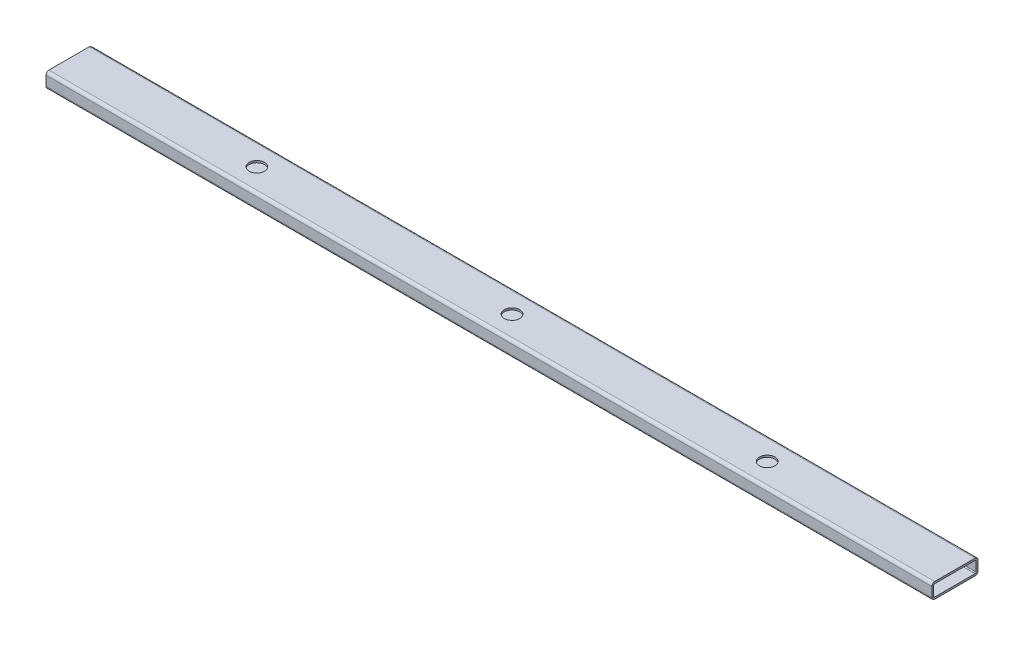
SolidWorks part; units mm, degrees
ref_plane "Front Plane" through (0, 0, 0) normal (0, 0, 1) x (1, 0, 0)
ref_plane "Top Plane" through (0, 0, 0) normal (0, 1, 0) x (1, 0, 0)
ref_plane "Right Plane" through (0, 0, 0) normal (1, 0, 0) x (0, 0, -1)
sketch "Sketch1" plane through (0, 0, 0) normal (1, 0, 0) x (0, 0, -1)
  line L0 (33.3248, 22.225) -> (-33.3248, 22.225)
  line L1 (33.3248, 25.4) -> (-33.3248, 25.4)
  line L2 (38.1, 20.6248) -> (38.1, 4.7752)
  line L3 (33.3248, 0) -> (-33.3248, 0)
  line L4 (-38.1, 20.6248) -> (-38.1, 4.7752)
  line L5 (-34.925, 20.6248) -> (-34.925, 4.7752)
  line L6 (33.3248, 3.175) -> (-33.3248, 3.175)
  line L7 (34.925, 20.6248) -> (34.925, 4.7752)
  arc A0 (38.1, 20.6248) -> (33.3248, 25.4) centre (33.3248, 20.6248) ccw
  arc A1 (38.1, 4.7752) -> (33.3248, 0) centre (33.3248, 4.7752) cw
  arc A2 (-33.3248, 0) -> (-38.1, 4.7752) centre (-33.3248, 4.7752) cw
  arc A3 (-38.1, 20.6248) -> (-33.3248, 25.4) centre (-33.3248, 20.6248) cw
  arc A4 (-34.925, 20.6248) -> (-33.3248, 22.225) centre (-33.3248, 20.6248) cw
  arc A5 (-33.3248, 3.175) -> (-34.925, 4.7752) centre (-33.3248, 4.7752) cw
  arc A6 (34.925, 4.7752) -> (33.3248, 3.175) centre (33.3248, 4.7752) cw
  arc A7 (34.925, 20.6248) -> (33.3248, 22.225) centre (33.3248, 20.6248) ccw
  point P5 (0, 0)
  dimension "D1" = 4.7752
  dimension "D2" = 25.4
  dimension "D3" = 76.2
  dimension "D4" = 3.175
extrude "Boss-Extrude1" add sketch "Sketch1" along normal mid plane 1460.5
sketch "Sketch2" plane through (0, 25.4, 0) normal (0, 1, 0) x (1, 0, 0)
  circle A0 centre (-420.6875, 0) radius 12.7
  dimension "D1" = 420.6875
  dimension "D2" = 25.4
extrude "Cut-Extrude1" cut sketch "Sketch2" against normal up to next (3.175 mm away)
pattern_linear "LPattern1" count 3 spacing 420.6875 along (1, 0, 0) of "Cut-Extrude1"
